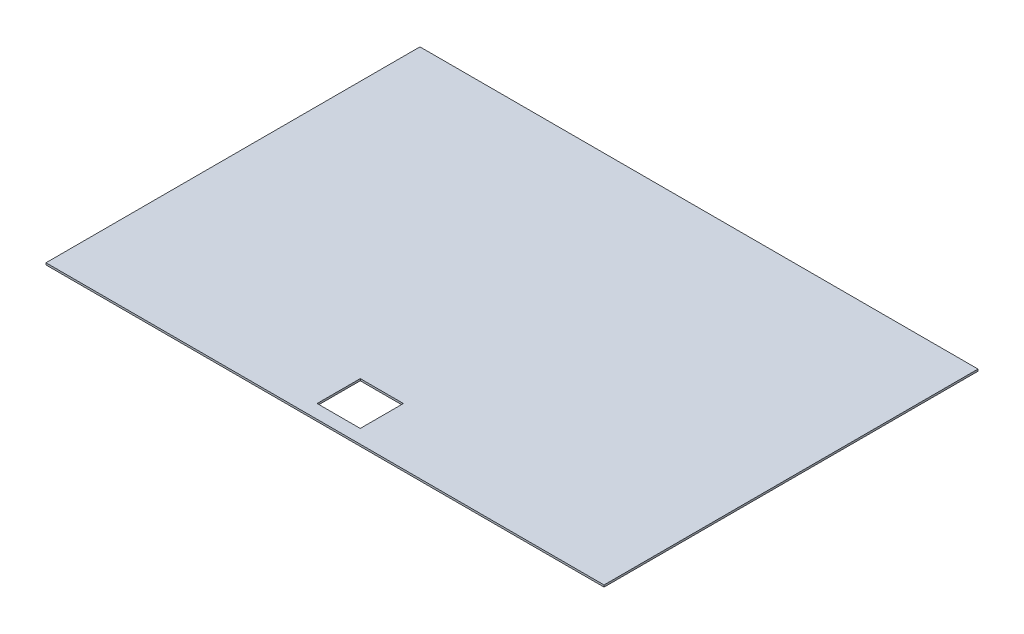
SolidWorks part; units mm, degrees
material "Acrylic (Medium-high impact)"
ref_plane "Front Plane" through (0, 0, 0) normal (0, 0, 1) x (1, 0, 0)
ref_plane "Top Plane" through (0, 0, 0) normal (0, 1, 0) x (1, 0, 0)
ref_plane "Right Plane" through (0, 0, 0) normal (1, 0, 0) x (0, 0, -1)
sketch "Sketch1" plane through (0, 0, 0) normal (0, 1, 0) x (1, 0, 0)
  line L1 (0, 0) -> (923.925, 0)
  line L2 (0, 0) -> (0, 619.125)
  line L3 (0, 619.125) -> (923.925, 619.125)
  line L4 (923.925, 0) -> (923.925, 619.125)
  dimension "D1" = 923.925
  dimension "D2" = 619.125
extrude "Boss-Extrude1" add sketch "Sketch1" along normal blind 3.175 contours L2 L3 L4 L1
sketch "Sketch2" plane through (0, 3.175, 0) normal (0, 1, 0) x (1, 0, 0)
  line L0 (461.9625, 0) -> (461.9625, 619.125) construction
  line L1 (427.0375, 23.3998) -> (496.8875, 23.3998) construction
  line L2 (427.0375, 23.3998) -> (427.0375, 93.2497) construction
  line L3 (427.0375, 93.2497) -> (496.8875, 93.2497) construction
  line L4 (496.8875, 23.3998) -> (496.8875, 93.2497) construction
  line L5 (0, 0) -> (923.925, 0) construction
  line L6 (0, 619.125) -> (923.925, 619.125) construction
  line L7 (426.2438, 22.606) -> (497.6812, 22.606)
  line L8 (497.6812, 22.606) -> (497.6812, 94.0435)
  line L9 (426.2438, 94.0435) -> (497.6812, 94.0435)
  line L10 (426.2438, 22.606) -> (426.2438, 94.0435)
  line L11 (427.0375, 93.2497) -> (461.9625, 23.3998) construction
  point P10 (461.9625, 23.3998)
  point P17 (498.475, 28.781)
  point P18 (0, 0)
  dimension "D1" = 69.85
  dimension "D3" = 22.606
  dimension "D2" = 0.7937
extrude "Cut-Extrude1" cut sketch "Sketch2" against normal through all both and the other way through all
